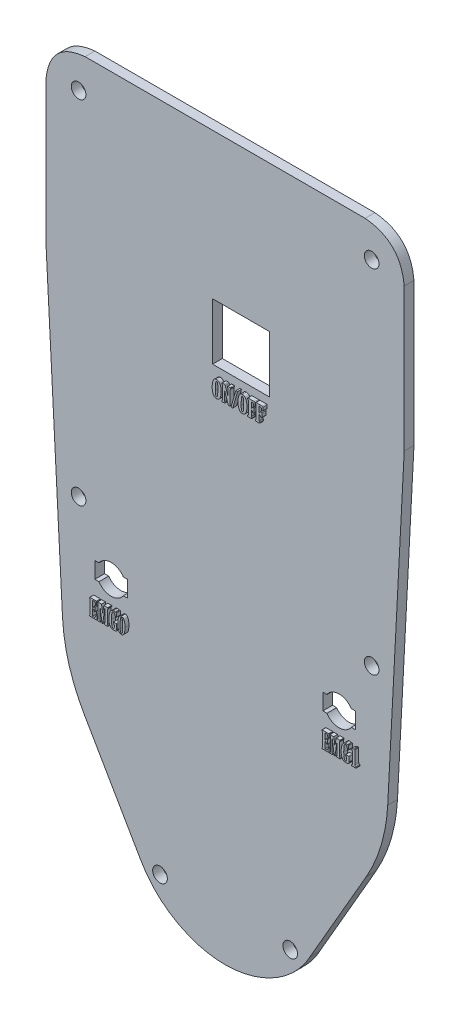
SolidWorks part; units mm, degrees
ref_plane "Front Plane" through (0, 0, 0) normal (0, 0, 1) x (1, 0, 0)
ref_plane "Top Plane" through (0, 0, 0) normal (0, 1, 0) x (1, 0, 0)
ref_plane "Right Plane" through (0, 0, 0) normal (1, 0, 0) x (0, 0, -1)
sketch "Model" plane through (0, 0, 0) normal (0, 0, 1) x (1, 0, 0)
  line L0 (55, 98) -> (55, 54.0964)
  line L1 (55, 54.0964) -> (49.9315, -42.6168)
  line L2 (43.3013, -65) -> (25.9808, -95)
  line L3 (-25.9808, -95) -> (-43.3013, -65)
  line L4 (-49.9315, -42.6168) -> (-55, 54.0964)
  line L5 (-55, 54.0964) -> (-55, 98)
  line L6 (-43, 110) -> (43, 110)
  line L7 (13.5591, 65.1953) -> (-3.8409, 65.1953)
  line L8 (-40, -22.5) -> (-40, -27.5)
  line L9 (-40, -27.5) -> (-38.7417, -27.5)
  line L10 (-31.2583, -27.5) -> (-30, -27.5)
  line L11 (-30, -27.5) -> (-30, -22.5)
  line L12 (-30, -22.5) -> (-31.2583, -22.5)
  line L13 (-38.7417, -22.5) -> (-40, -22.5)
  line L14 (0, 2.5) -> (0, 20)
  line L15 (31.2583, -22.5) -> (30, -22.5)
  line L16 (30, -22.5) -> (30, -27.5)
  line L17 (30, -27.5) -> (31.2583, -27.5)
  line L18 (38.7417, -27.5) -> (40, -27.5)
  line L19 (40, -27.5) -> (40, -22.5)
  line L20 (40, -22.5) -> (38.7417, -22.5)
  line L21 (13.5591, 47.7953) -> (13.5591, 65.1953)
  line L22 (-3.8409, 47.7953) -> (13.5591, 47.7953)
  line L23 (-3.8409, 65.1953) -> (-3.8409, 47.7953)
  line L24 (14.0591, 47.2953) -> (14.0591, 65.6953)
  line L25 (14.0591, 65.6953) -> (-4.3409, 65.6953)
  line L26 (-4.3409, 65.6953) -> (-4.3409, 47.2953)
  line L27 (-4.3409, 47.2953) -> (14.0591, 47.2953)
  circle A0 centre (-45, 100) radius 2.25
  circle A1 centre (45, 100) radius 2.25
  circle A2 centre (-45, -7.9998) radius 2.25
  circle A3 centre (45, -7.9998) radius 2.25
  circle A4 centre (-35, -25) radius 5.5902
  circle A5 centre (-35, -25) radius 4.5
  circle A6 centre (-20, -96) radius 2.25
  circle A7 centre (20, -96) radius 2.25
  arc A8 (43.3013, -65) -> (49.9315, -42.6168) centre (0, -40) ccw
  arc A9 (-25.9808, -95) -> (25.9808, -95) centre (0, -80) ccw
  arc A10 (-49.9315, -42.6168) -> (-43.3013, -65) centre (0, -40) ccw
  arc A11 (-43, 110) -> (-55, 98) centre (-43, 98) ccw
  arc A12 (55, 98) -> (43, 110) centre (43, 98) ccw
  arc A13 (-38.7417, -27.5) -> (-31.2583, -27.5) centre (-35, -25) ccw
  arc A14 (-31.2583, -22.5) -> (-38.7417, -22.5) centre (-35, -25) ccw
  arc A15 (38.7417, -22.5) -> (31.2583, -22.5) centre (35, -25) ccw
  arc A16 (31.2583, -27.5) -> (38.7417, -27.5) centre (35, -25) ccw
  point P58 (0, 0)
  point P59 (0, 0)
  point P60 (0, 0)
  point P61 (0, 0)
  point P62 (0, 0)
sketch "Sketch2" plane through (0, 0, 0) normal (0, 0, 1) x (1, 0, 0)
  line L0 (43, 110) -> (-43, 110)
  line L1 (-55, 98) -> (-55, 54.0964)
  line L2 (-55, 54.0964) -> (-49.9315, -42.6168)
  line L3 (-43.3013, -65) -> (-25.9808, -95)
  line L5 (25.9808, -95) -> (43.3013, -65)
  line L8 (49.9315, -42.6168) -> (55, 54.0964)
  line L9 (55, 54.0964) -> (55, 98)
  arc A0 (-25.9808, -95) -> (25.9808, -95) centre (0, -80) ccw construction
  arc A4 (55, 98) -> (43, 110) centre (43, 98) ccw construction
  arc A5 (-43, 110) -> (-55, 98) centre (-43, 98) ccw construction
  arc A6 (-49.9315, -42.6168) -> (-43.3013, -65) centre (0, -40) ccw construction
  arc A20 (43.3013, -65) -> (49.9315, -42.6168) centre (0, -40) ccw construction
  spline S0 degree 2 poles (-43, 110) (-53.9706, 108.9706) (-55, 98) knots 0 0 0 1 1 1
  spline S1 degree 2 poles (43, 110) (53.9706, 108.9706) (55, 98) knots 0 0 0 1 1 1
  spline S2 degree 2 poles (-49.9315, -42.6168) (-49.2656, -54.5931) (-43.3013, -65) knots 0 0 0 1 1 1
  spline S3 degree 2 poles (49.9315, -42.6168) (49.2656, -54.5931) (43.3013, -65) knots 0 0 0 1 1 1
  spline S4 degree 3 poles (-25.9808, -95) (-20.804, -104.373) (-0.0255, -115.6511) (20.8833, -104.3248) (25.9808, -95) knots 0 0 0 0 0.49983 1 1 1 1
extrude "Boss-Extrude1" add sketch "Sketch2" along normal blind 3
sketch "Sketch3" plane through (0, 0, 0) normal (0, 0, 1) x (1, 0, 0)
  circle A0 centre (-45, 100) radius 2.25
  circle A1 centre (45, 100) radius 2.25
  circle A2 centre (45, -7.9998) radius 2.25
  circle A3 centre (20, -96) radius 2.25
  circle A4 centre (-20, -96) radius 2.25
  circle A5 centre (-45, -7.9998) radius 2.25
extrude "Cut-Extrude1" cut sketch "Sketch3" along normal blind 5
sketch "Sketch4" plane through (0, 0, 0) normal (0, 0, 1) x (1, 0, 0)
  line L0 (31.2583, -22.5) -> (30, -22.5)
  line L1 (30, -22.5) -> (30, -27.5)
  line L2 (30, -27.5) -> (31.2583, -27.5)
  line L3 (38.7417, -22.5) -> (40, -22.5)
  line L4 (40, -22.5) -> (40, -27.5)
  line L5 (40, -27.5) -> (38.7417, -27.5)
  line L7 (-38.7417, -22.5) -> (-40, -22.5)
  line L8 (-40, -22.5) -> (-40, -27.5)
  line L9 (-40, -27.5) -> (-38.7417, -27.5)
  line L10 (-31.2583, -27.5) -> (-30, -27.5)
  line L11 (-30, -27.5) -> (-30, -22.5)
  line L12 (-30, -22.5) -> (-31.2583, -22.5)
  arc A0 (38.7417, -22.5) -> (31.2583, -22.5) centre (35, -25) ccw
  arc A1 (38.7417, -22.5) -> (31.2583, -22.5) centre (35, -25) ccw construction
  arc A2 (38.7417, -27.5) -> (31.2583, -27.5) centre (35, -25) cw
  arc A3 (31.2583, -27.5) -> (38.7417, -27.5) centre (35, -25) ccw construction
  arc A4 (-31.2583, -22.5) -> (-38.7417, -22.5) centre (-35, -25) ccw
  arc A5 (-38.7417, -27.5) -> (-31.2583, -27.5) centre (-35, -25) ccw
  point P39 (0, 0)
  point P43 (-38.7417, -22.5014)
extrude "Cut-Extrude5" cut sketch "Sketch4" along normal blind 4
sketch "Sketch7" plane through (0, 0, 0) normal (0, 0, 1) x (1, 0, 0)
  line L1 (-3.8409, 65.1953) -> (13.5591, 65.1953)
  line L2 (-3.8409, 65.1953) -> (-3.8409, 47.7953)
  line L3 (-3.8409, 47.7953) -> (13.5591, 47.7953)
  line L4 (13.5591, 65.1953) -> (13.5591, 47.7953)
extrude "Cut-Extrude6" cut sketch "Sketch7" along normal blind 4
sketch "Sketch8" plane through (0, 0, 0) normal (0, 0, 1) x (1, 0, 0)
  text T0 "<b>ON/OFF</b>" font "Gloucester MT Extra Condensed" height 5
extrude "Boss-Extrude2" add sketch "Sketch8" along normal blind 4.2
sketch "Sketch9" plane through (0, 0, 0) normal (0, 0, 1) x (1, 0, 0)
  text T0 "EMG0" font "Gloucester MT Extra Condensed" height 5
  text T1 "EMG1" font "Gloucester MT Extra Condensed" height 5
extrude "Boss-Extrude4" add sketch "Sketch9" along normal blind 4.2
